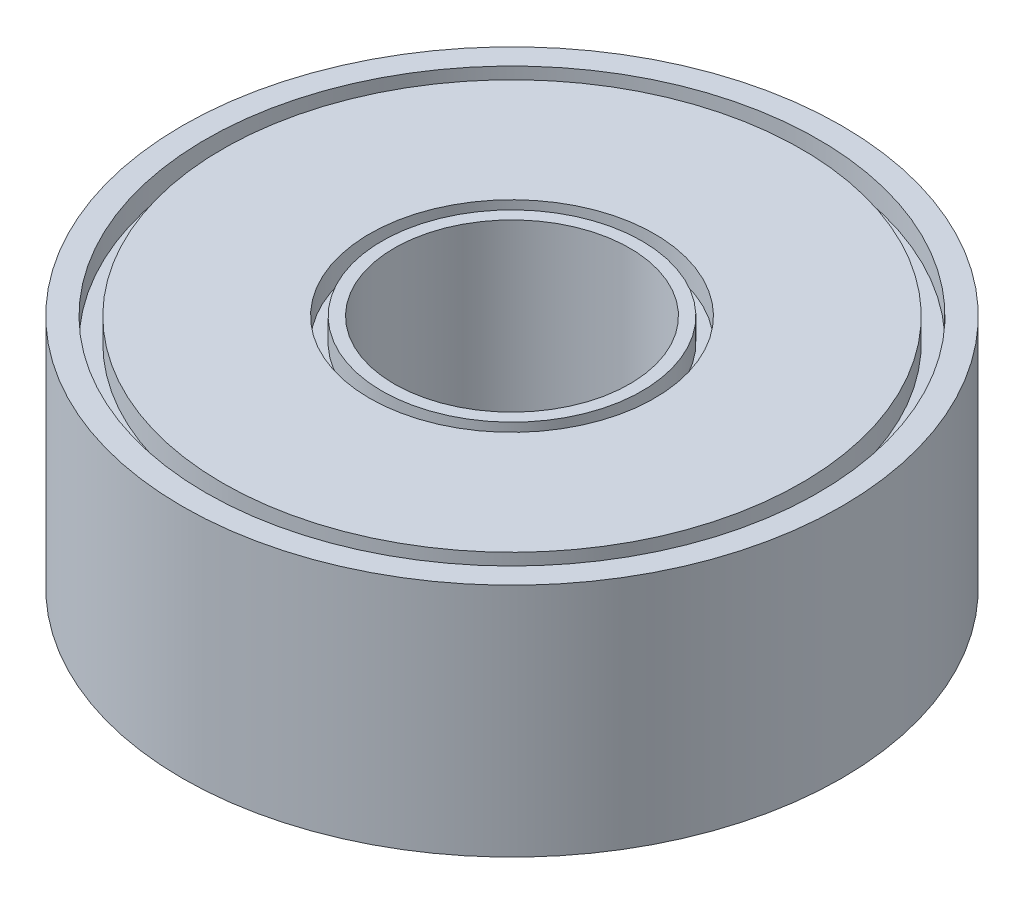
SolidWorks part; units mm, degrees
ref_plane "Front Plane" through (0, 0, 0) normal (0, 0, 1) x (1, 0, 0)
ref_plane "Top Plane" through (0, 0, 0) normal (0, 1, 0) x (1, 0, 0)
ref_plane "Right Plane" through (0, 0, 0) normal (1, 0, 0) x (0, 0, -1)
sketch "Sketch1" plane through (0, 0, 0) normal (0, 1, 0) x (1, 0, 0)
  circle A0 centre (0, 0) radius 7
  circle A1 centre (0, 0) radius 2.5
  dimension "D1" = 14
  dimension "D2" = 5
extrude "Boss-Extrude1" add sketch "Sketch1" along normal blind 5
sketch "Sketch2" plane through (0, 5, 0) normal (0, 1, 0) x (1, 0, 0)
  circle A0 centre (0, 0) radius 2.7602
  circle A1 centre (0, 0) radius 3.0247
extrude "Cut-Extrude1" cut sketch "Sketch2" against normal blind 0.5
sketch "Sketch3" plane through (0, 5, 0) normal (0, 1, 0) x (1, 0, 0)
  circle A0 centre (0, 0) radius 6.501
  circle A1 centre (0, 0) radius 6.1437
extrude "Cut-Extrude2" cut sketch "Sketch3" against normal blind 0.5
sketch "Sketch4" plane through (0, 0, 0) normal (0, -1, 0) x (1, 0, 0)
  circle A0 centre (0, 0) radius 2.9149
  circle A1 centre (0, 0) radius 3.2119
  circle A2 centre (0, 0) radius 6.6537
  circle A3 centre (0, 0) radius 6.403
extrude "Cut-Extrude3" cut sketch "Sketch4" against normal blind 0.5 contours A1 | A0 | A3 | A2
